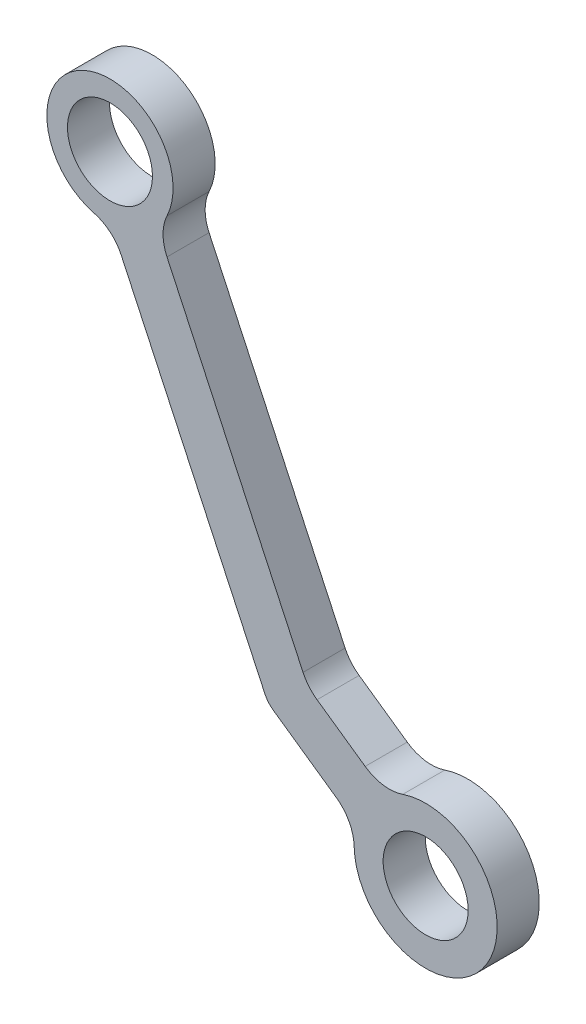
SolidWorks part; units mm, degrees
material "ABS"
ref_plane "Plan de face" through (0, 0, 0) normal (0, 0, 1) x (1, 0, 0)
ref_plane "Plan de dessus" through (0, 0, 0) normal (0, 1, 0) x (1, 0, 0)
ref_plane "Plan de droite" through (0, 0, 0) normal (1, 0, 0) x (0, 0, -1)
sketch "Esquisse2" plane through (-37.9087, 0, 1.2459) normal (0, 0, 1) x (1, 0, 0)
  line L0 (39.6108, -12.6653) -> (61.2919, -59.1607)
  line L1 (37.9087, 0) -> (64.745, -57.5505) construction
  line L2 (92.9087, 0) -> (-17.0913, 0) construction
  line L3 (67.0475, -53.4731) -> (46.5168, -9.4449)
  line L4 (64.745, -57.5505) -> (85.5514, -72.1194) construction
  line L5 (62.5596, -60.6715) -> (72.0533, -67.3191)
  line L6 (69.1603, -55.9911) -> (76.424, -61.0771)
  circle A0 centre (37.9087, 0) radius 6.4135
  arc A1 (46.5266, -4.0568) -> (35.4769, -9.2093) centre (37.9087, 0) ccw
  circle A3 centre (85.5514, -72.1194) radius 6.4135
  arc A6 (74.7594, -72.3721) -> (82.0978, -61.8918) centre (85.5514, -72.1194) ccw
  arc A7 (61.2919, -59.1607) -> (62.5596, -60.6715) centre (64.745, -57.5505) ccw
  arc A8 (46.5168, -9.4449) -> (46.5266, -4.0568) centre (52.2719, -6.7613) cw
  arc A9 (39.6108, -12.6653) -> (35.4769, -9.2093) centre (33.8557, -15.3489) ccw
  arc A10 (67.0475, -53.4731) -> (69.1603, -55.9911) centre (72.8025, -50.7894) ccw
  arc A11 (76.424, -61.0771) -> (82.0978, -61.8918) centre (80.0662, -55.8755) ccw
  arc A12 (72.0533, -67.3191) -> (74.7594, -72.3721) centre (68.4111, -72.5207) cw
  point P29 (79.4631, -63.2051)
  point P32 (75.0924, -69.4471)
  dimension "D1" = 12.827
  dimension "D2" = 25.4
  dimension "D3" = 9.525
  dimension "D5" = 10.795
  dimension "D6" = 6.35
  dimension "D11" = 3.81
  dimension "D13" = 12.827
  dimension "D4" = 63.5
  dimension "D7" = 150
  dimension "D8" = 3.81
  dimension "D9" = 3.81
  dimension "D10" = 3.81
  dimension "D12" = 65
extrude "Boss.-Extru.1" add sketch "Esquisse2" along normal blind 6.35
